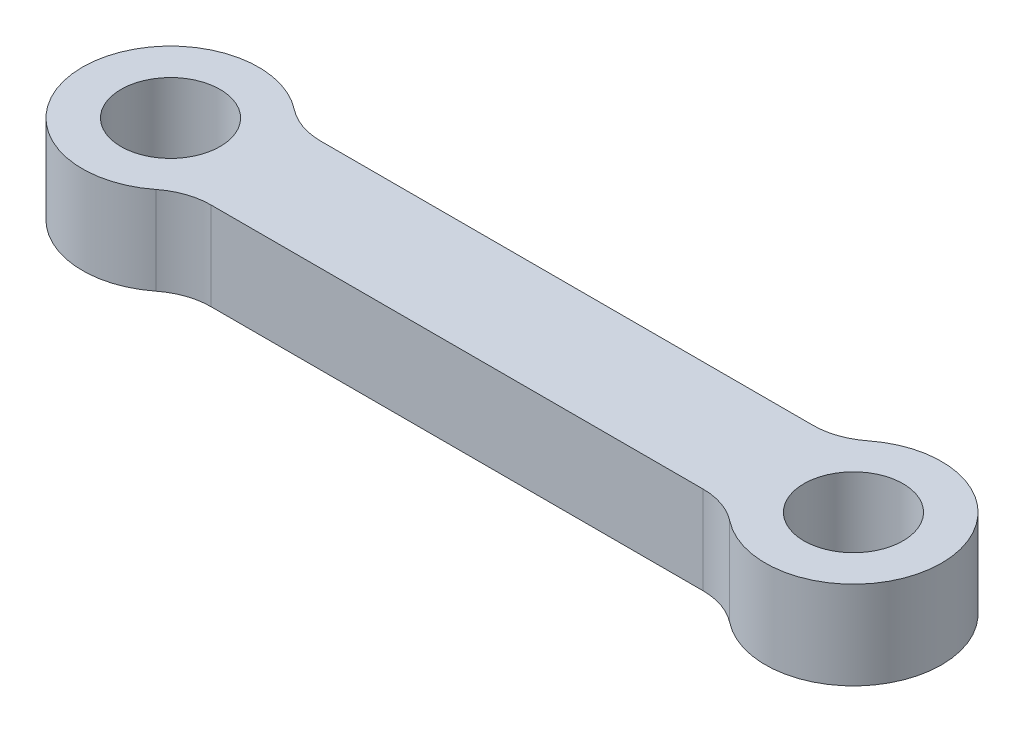
SolidWorks part; units mm, degrees
ref_plane "Front Plane" through (0, 0, 0) normal (0, 0, 1) x (1, 0, 0)
ref_plane "Top Plane" through (0, 0, 0) normal (0, 1, 0) x (1, 0, 0)
ref_plane "Right Plane" through (0, 0, 0) normal (1, 0, 0) x (0, 0, -1)
sketch "Sketch1" plane through (0, 0, 0) normal (0, 1, 0) x (1, 0, 0)
  line L0 (0, 0) -> (31, 0) construction
  line L1 (3.1225, 2.5) -> (27.8775, 2.5)
  line L2 (3.1225, -2.5) -> (27.8775, -2.5)
  circle A0 centre (0, 0) radius 4
  circle A1 centre (31, 0) radius 4
  circle A2 centre (0, 0) radius 2.25
  circle A3 centre (31, 0) radius 2.25
  dimension "D1" = 8
  dimension "D3" = 8
  dimension "D5" = 4.5
  dimension "D2" = 31
  dimension "D4" = 2.5
extrude "Boss-Extrude1" add sketch "Sketch1" along normal blind 4
fillet "Fillet1" radius 3 4 edges at (3.1225, 2, 2.5) (27.8775, 2, 2.5) (27.8775, 2, -2.5) (3.1225, 2, -2.5)
